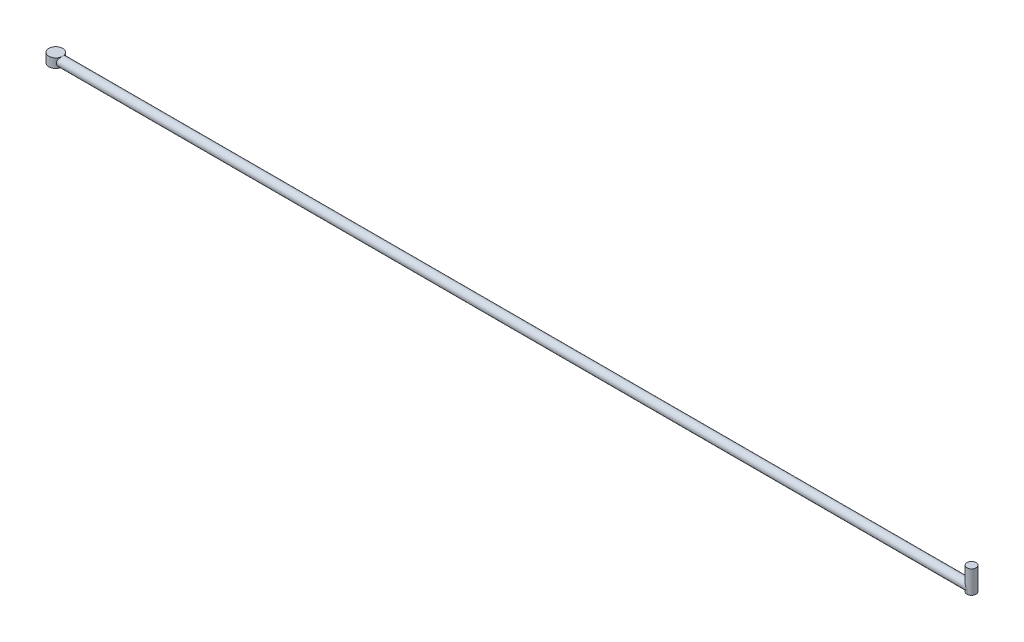
SolidWorks part; units mm, degrees
ref_plane "Front" through (0, 0, 0) normal (0, 0, 1) x (1, 0, 0)
ref_plane "Top" through (0, 0, 0) normal (0, 1, 0) x (1, 0, 0)
ref_plane "Right" through (0, 0, 0) normal (1, 0, 0) x (0, 0, -1)
sketch "Sketch1" plane through (0, 0, 0) normal (0, 1, 0) x (1, 0, 0)
  circle A0 centre (0, 0) radius 15
extrude "Boss-Extrude1" add sketch "Sketch1" along normal blind 20
sketch "Sketch2" plane through (0, 0, 0) normal (1, 0, 0) x (0, 0, -1)
  line L0 (0, 0) -> (0, 20) construction
  line L1 (15, 20) -> (-15, 20) construction
  circle A0 centre (0, 10) radius 10
extrude "Boss-Extrude2" add sketch "Sketch2" along normal blind 2000
sketch "Sketch3" plane through (0, 0, 0) normal (0, 1, 0) x (1, 0, 0)
  line L0 (2000, -10) -> (2000, 10) construction
  circle A0 centre (2000, 0) radius 10
extrude "Boss-Extrude3" add sketch "Sketch3" along normal blind 50
